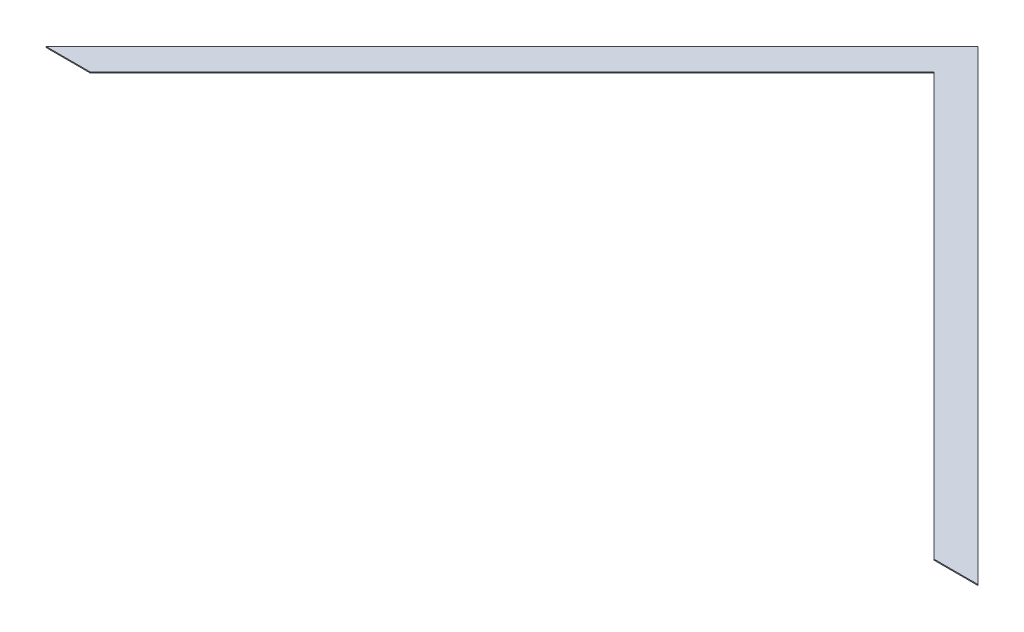
SolidWorks part; units mm, degrees
ref_plane "Front Plane" through (0, 0, 0) normal (0, 0, 1) x (1, 0, 0)
ref_plane "Top Plane" through (0, 0, 0) normal (0, 1, 0) x (1, 0, 0)
ref_plane "Right Plane" through (0, 0, 0) normal (1, 0, 0) x (0, 0, -1)
sketch "Sketch1" plane through (0, 0, 0) normal (0, 1, 0) x (1, 0, 0)
  line L6 (0, 0) -> (762, 762)
  line L7 (762, 762) -> (1524, 0)
  line L10 (1524, 0) -> (1452.158, 0)
  line L11 (1452.158, 0) -> (762, 690.158)
  line L12 (762, 690.158) -> (71.842, 0)
  line L13 (71.842, 0) -> (0, 0)
  line L14 (762, 762) -> (762, 0) construction
  dimension "D2" = 1524
  dimension "D3" = 762
  dimension "D1" = 50.8
  dimension "D4" = 90
extrude "Boss-Extrude1" add sketch "Sketch1" along normal blind 1.5875
